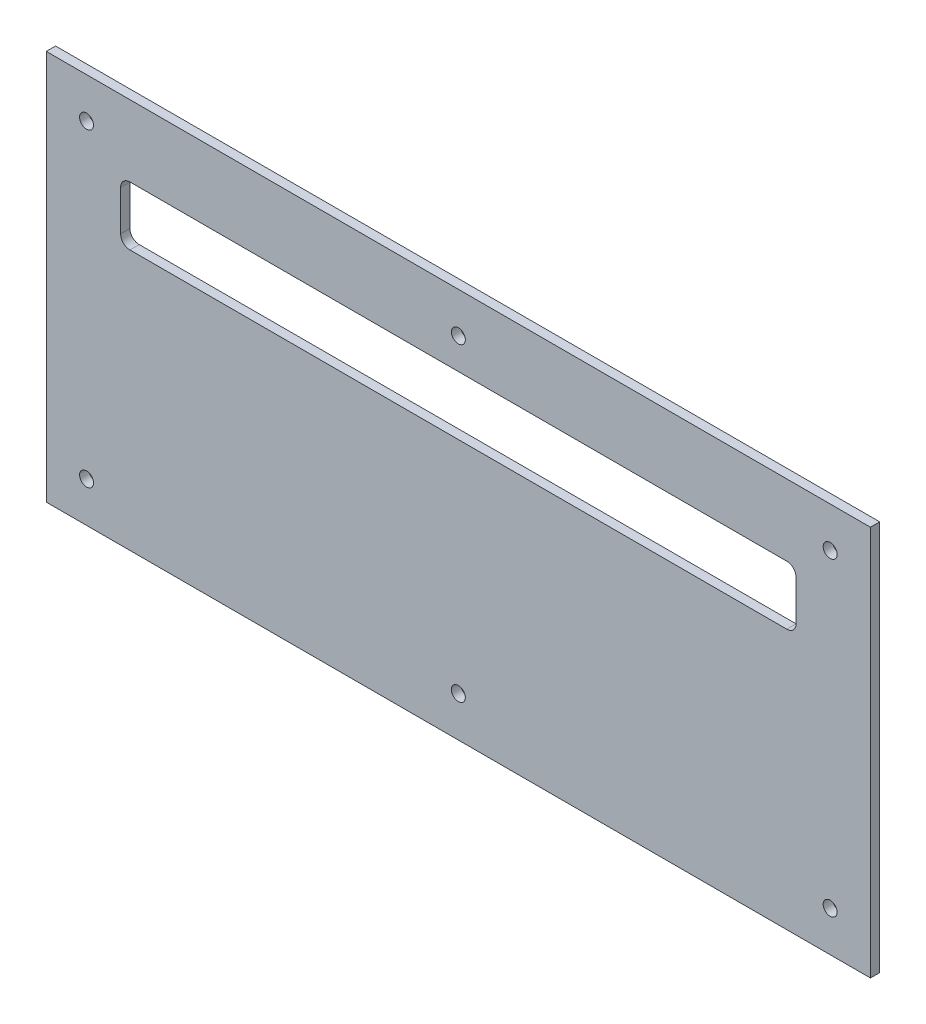
SolidWorks part; units mm, degrees
ref_plane "Спереди" through (0, 0, 0) normal (0, 0, 1) x (1, 0, 0)
ref_plane "Сверху" through (0, 0, 0) normal (0, 1, 0) x (1, 0, 0)
ref_plane "Справа" through (0, 0, 0) normal (1, 0, 0) x (0, 0, -1)
sketch "Эскиз1" plane through (0, 0, 0) normal (0, 0, -1) x (-1, 0, 0)
  line L0 (-23, 123) -> (243, 123)
  line L1 (-23, 123) -> (-23, -3)
  line L2 (243, 123) -> (243, -3)
  line L3 (-23, -3) -> (243, -3)
  line L4 (-23, -3) -> (-23, 123) construction
  line L5 (-20, 123) -> (240, 123) construction
  line L6 (243, 123) -> (243, -3) construction
  line L7 (240, -3) -> (-20, -3) construction
extrude "Бобышка-Вытянуть1" add sketch "Эскиз1" along normal blind 3
sketch "Эскиз2" plane through (0, 0, 0) normal (0, 0, 1) x (1, 0, 0)
  line L4 (-220, 100) -> (-220, 81)
  line L5 (0, 100) -> (-220, 100)
  line L6 (0, 81) -> (0, 100)
  line L7 (-220, 81) -> (0, 81)
  line L8 (-220, 100) -> (-220, 81)
  line L9 (0, 100) -> (-220, 100)
  line L10 (0, 81) -> (0, 100)
  line L11 (-220, 81) -> (0, 81)
  dimension "D1" = 0
extrude "Вырез-Вытянуть1" cut sketch "Эскиз2" against normal through all
sketch "Эскиз3" plane through (0, 0, 0) normal (-1, 0, 0) x (0, 0, 1)
  line L4 (0, 81) -> (0, 100)
  line L5 (0, 100) -> (-3, 100)
  line L6 (-3, 100) -> (-3, 81)
  line L7 (-3, 81) -> (0, 81)
  line L8 (0, 81) -> (0, 100)
  line L9 (0, 100) -> (-3, 100)
  line L10 (-3, 100) -> (-3, 81)
  line L11 (-3, 81) -> (0, 81)
  dimension "D1" = 0
extrude "Бобышка-Вытянуть2" add sketch "Эскиз3" along normal blind 1
sketch "Эскиз4" plane through (-220, 0, 0) normal (1, 0, 0) x (0, 0, -1)
  line L4 (0, 100) -> (0, 81)
  line L5 (0, 81) -> (3, 81)
  line L6 (3, 81) -> (3, 100)
  line L7 (3, 100) -> (0, 100)
  line L8 (0, 100) -> (0, 81)
  line L9 (0, 81) -> (3, 81)
  line L10 (3, 81) -> (3, 100)
  line L11 (3, 100) -> (0, 100)
  dimension "D1" = 0
extrude "Бобышка-Вытянуть3" add sketch "Эскиз4" along normal blind 1
fillet "Скругление1" radius 3 4 edges at (-219, 81, -1.5) (-219, 100, -1.5) (-1, 100, -1.5) (-1, 81, -1.5)
sketch "Эскиз5" plane through (0, 0, -3) normal (0, 0, -1) x (-1, 0, 0)
  circle A0 centre (230, 110) radius 2.25 construction
  circle A1 centre (230, 110) radius 2.25
  circle A2 centre (110, 110) radius 2.25 construction
  circle A3 centre (110, 110) radius 2.25
  circle A4 centre (-10, 110) radius 2.25 construction
  circle A5 centre (-10, 110) radius 2.25
  circle A6 centre (-10, 10) radius 2.25 construction
  circle A7 centre (-10, 10) radius 2.25
  circle A8 centre (110, 10) radius 2.25 construction
  circle A9 centre (110, 10) radius 2.25
  circle A10 centre (230, 10) radius 2.25 construction
  circle A11 centre (230, 10) radius 2.25
extrude "Вырез-Вытянуть2" cut sketch "Эскиз5" against normal through all
